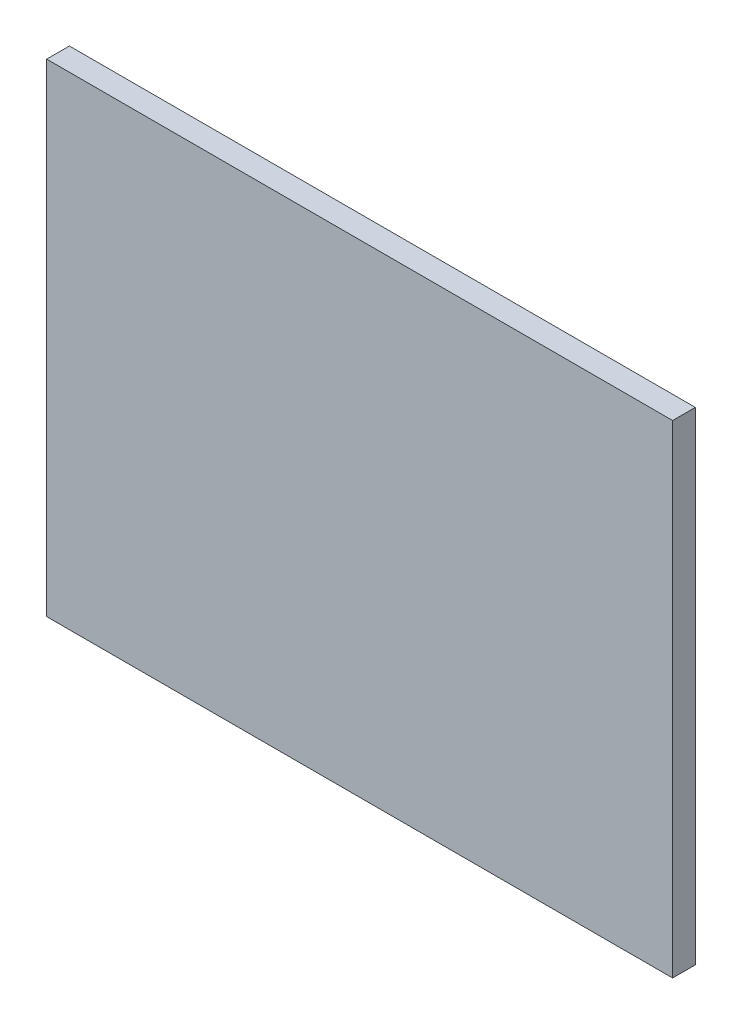
SolidWorks part; units mm, degrees
material "Acrylic (Medium-high impact)"
ref_plane "Front Plane" through (0, 0, 0) normal (0, 0, 1) x (1, 0, 0)
ref_plane "Top Plane" through (0, 0, 0) normal (0, 1, 0) x (1, 0, 0)
ref_plane "Right Plane" through (0, 0, 0) normal (1, 0, 0) x (0, 0, -1)
sketch "Sketch1" plane through (0, 0, 0) normal (0, 0, 1) x (1, 0, 0)
  line L1 (-43.735, 33.735) -> (43.735, 33.735)
  line L2 (-43.735, 33.735) -> (-43.735, -33.735)
  line L3 (-43.735, -33.735) -> (43.735, -33.735)
  line L4 (43.735, 33.735) -> (43.735, -33.735)
  line L5 (-43.735, 33.735) -> (43.735, -33.735) construction
  line L6 (-43.735, -33.735) -> (43.735, 33.735) construction
  point P0 (0, 0)
  dimension "D1" = 87.47
  dimension "D2" = 67.47
extrude "Boss-Extrude1" add sketch "Sketch1" along normal blind 3.175
equation "\"length\"=87.3"
equation "\"D1@Sketch1\"=\"length\" + 2*\"kerf\""
equation "\"width\"=67.3"
equation "\"D2@Sketch1\"=\"width\" + 2*\"kerf\""
equation "\"depth\"=3.175"
equation "\"D1@Boss-Extrude1\"=\"depth\""
equation "\"kerf\"= 0.17 / 2mm"
